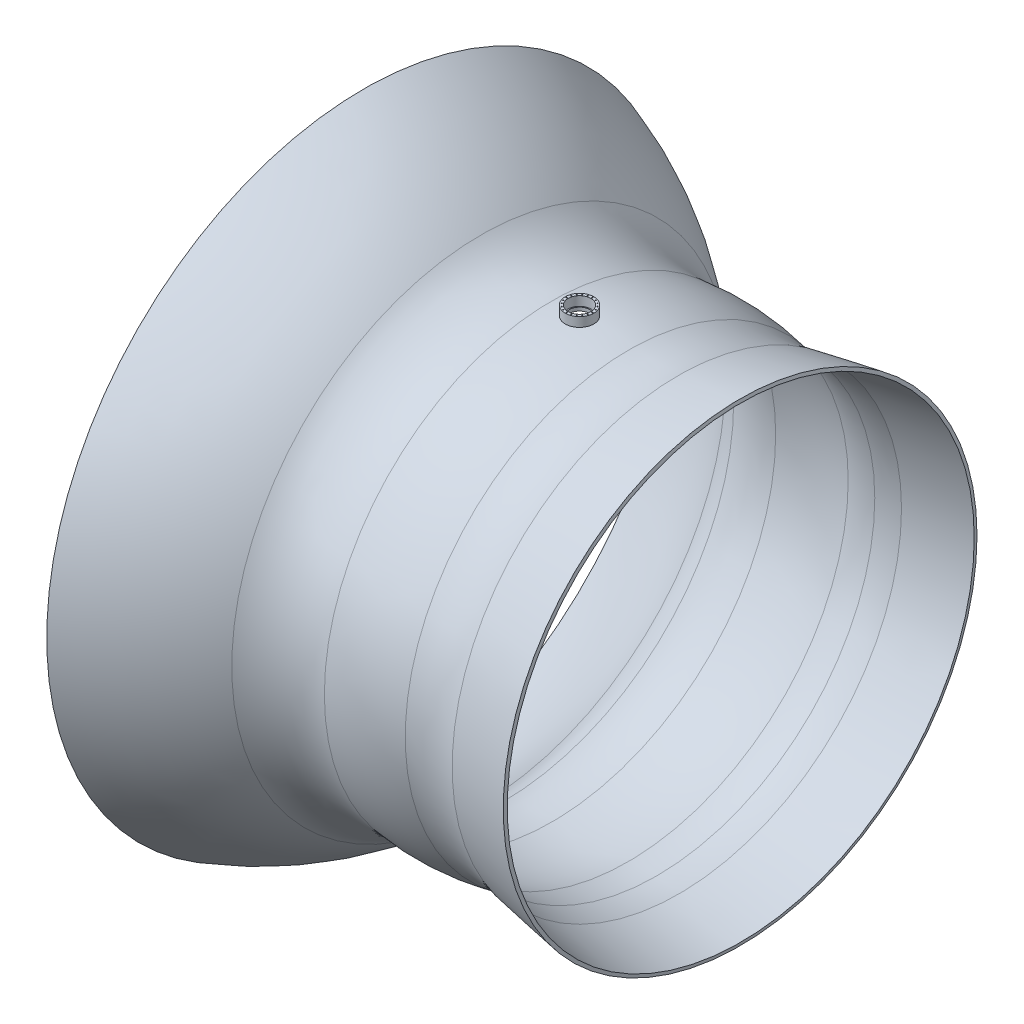
SolidWorks part; units mm, degrees
ref_plane "Plano frontal" through (0, 0, 0) normal (0, 0, 1) x (1, 0, 0)
ref_plane "Plano superior" through (0, 0, 0) normal (0, 1, 0) x (1, 0, 0)
ref_plane "Plano direito" through (0, 0, 0) normal (1, 0, 0) x (0, 0, -1)
sketch "Esboço1" plane through (0, 0, 0) normal (0, 0, 1) x (1, 0, 0)
  line L0 (0, 0) -> (0, 3950) construction
  line L1 (0, 0) -> (8940.3328, 0) construction
  line L2 (2824, 4091) -> (1741, 3900)
  line L3 (2813.5791, 4150.0881) -> (1726.4789, 3958.365)
  line L4 (-3781.2155, 5552.9837) -> (-3800, 5496)
  line L5 (2813.5791, 4150.0881) -> (2824, 4091)
  arc A0 (849.5312, 3857.5636) -> (1741, 3900) centre (1216.8727, 5525.5936) ccw
  arc A1 (849.5312, 3857.5636) -> (-483.402, 3920.309) centre (0, 0) ccw
  arc A2 (-1766.2512, 4321.5538) -> (-483.402, 3920.309) centre (-682.5146, 5535.0793) ccw
  arc A3 (862.4354, 3916.1595) -> (1726.4789, 3958.365) centre (1216.8727, 5525.5936) ccw
  arc A4 (-1766.2512, 4321.5538) -> (-3800, 5496) centre (-5603.6244, 24.6144) ccw
  arc A5 (862.4354, 3916.1595) -> (-490.7448, 3979.858) centre (0, 0) ccw
  arc A6 (-1726.2855, 4366.3058) -> (-490.7448, 3979.858) centre (-682.5146, 5535.0793) ccw
  arc A7 (-1726.2855, 4366.3058) -> (-3781.2155, 5552.9837) centre (-5603.6244, 24.6144) ccw
  point P13 (-3800, 5496)
  point P14 (-1760, 4316)
  dimension "D3" = 3416
  dimension "D4" = 3950
  dimension "D7" = 3254
  dimension "D8" = 5761
  dimension "D1" = 4091
  dimension "D2" = 3900
  dimension "D5" = 2824
  dimension "D6" = 1741
  dimension "D9" = 3800
  dimension "D10" = 5496
  dimension "D11" = 1760
  dimension "D12" = 4316
  dimension "D13" = 60
revolve "Revolução1" add sketch "Esboço1" angle 360 about L1
sketch "Esboço2" plane through (0, 0, 0) normal (0, 1, 0) x (1, 0, 0)
  circle A0 centre (0, 0) radius 180
  dimension "D1" = 360
extrude "Corte-extrusão1" cut sketch "Esboço2" along normal through all
sketch "Esboço3" plane through (0, 0, 0) normal (0, 1, 0) x (1, 0, 0)
  circle A0 centre (0, 0) radius 200
  circle A1 centre (0, 0) radius 250
  dimension "D1" = 400
  dimension "D2" = 500
extrude "Ressalto-extrusão1" add sketch "Esboço3" against normal up to surface (160.9906 mm away) from offset 4166
hole_wizard "Broca de rosquear para tarraxa de M20x2.01" positions "Esboço5" profile "Esboço4" hole size "M20x2.0" standard "DIN"
sketch "Esboço5" plane through (0, 4166, 0) normal (0, 1, 0) x (1, 0, 0)
  line L0 (0, 200) -> (0, 250) construction
  circle A0 centre (0, 0) radius 200 construction
  circle A1 centre (0, 0) radius 200 construction
  circle A2 centre (0, 0) radius 250 construction
  point P0 (0, 225)
  point P14 (0, 225)
  point P21 (69.5288, 213.9877)
  point P22 (132.2517, 182.0288)
  point P23 (182.0288, 132.2517)
  point P24 (213.9877, 69.5288)
  point P25 (225, 0)
  point P26 (213.9877, -69.5288)
  point P27 (182.0288, -132.2517)
  point P28 (132.2517, -182.0288)
  point P29 (69.5288, -213.9877)
  point P30 (0, -225)
  point P31 (-69.5288, -213.9877)
  point P32 (-132.2517, -182.0288)
  point P33 (-182.0288, -132.2517)
  point P34 (-213.9877, -69.5288)
  point P35 (-225, 0)
  point P36 (-213.9877, 69.5288)
  point P37 (-182.0288, 132.2517)
  point P38 (-132.2517, 182.0288)
  point P39 (-69.5288, 213.9877)
  point P40 (0, 0)
  dimension "D1" = 20
sketch "Esboço4" plane through (0, 4166, -225) normal (1, 0, 0) x (0, 0, 1)
  line L0 (0, 0) -> (0, 57.4077)
  line L1 (0, 57.4077) -> (9, 52)
  line L2 (9, 52) -> (9, 0)
  line L5 (9, 0) -> (0, 0)
  line L10 (0, 57.4077) -> (-9, 52) construction
  line L11 (0, -6.35) -> (0, 107.95) construction
  dimension "Hole Dia." = 18
  dimension "Hole Depth" = 52
  dimension "Drill Angle" = 118
sketch "Esboço6" plane through (0, 0, 0) normal (0, 0, 1) x (1, 0, 0)
  line L0 (0, 0) -> (3588.0907, 0) construction
  line L1 (-1350, -4051.3029) -> (-1350, 4051.3029)
  line L2 (1350, -3822.7897) -> (1350, 3822.7897)
  arc A0 (-1766.2512, 4321.5538) -> (-483.402, 3920.309) centre (-682.5146, 5535.0793) ccw construction
  arc A1 (849.5312, 3857.5636) -> (1741, 3900) centre (1216.8727, 5525.5936) ccw construction
  point P10 (-1350, 0)
  point P16 (1350, 0)
  dimension "D1" = 1350
  dimension "D2" = 1350
split line "Linha de divisão1"
